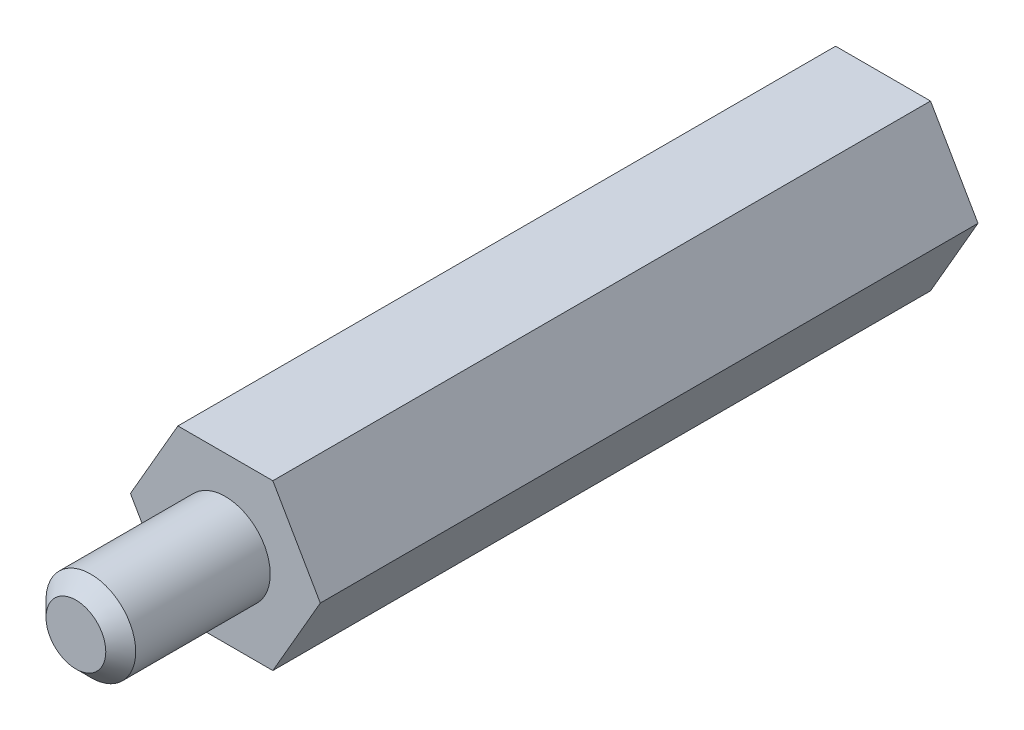
SolidWorks part; units mm, degrees
material "黄铜"
ref_plane "前视基准面" through (0, 0, 0) normal (0, 0, 1) x (1, 0, 0)
ref_plane "上视基准面" through (0, 0, 0) normal (0, 1, 0) x (1, 0, 0)
ref_plane "右视基准面" through (0, 0, 0) normal (1, 0, 0) x (0, 0, -1)
sketch "草图1" plane through (0, 0, 0) normal (0, 0, 1) x (1, 0, 0)
  line L1 (3.1754, 0) -> (1.5877, 2.75)
  line L2 (1.5877, 2.75) -> (-1.5877, 2.75)
  line L3 (-1.5877, 2.75) -> (-3.1754, 0)
  line L4 (-3.1754, 0) -> (-1.5877, -2.75)
  line L5 (-1.5877, -2.75) -> (1.5877, -2.75)
  line L6 (1.5877, -2.75) -> (3.1754, 0)
  circle A0 centre (0, 0) radius 2.75 construction
extrude "凸台-拉伸1" add sketch "草图1" along normal blind 22
sketch "草图2" plane through (0, 0, 22) normal (0, 0, 1) x (1, 0, 0)
  circle A0 centre (0, 0) radius 1.5
extrude "凸台-拉伸2" add sketch "草图2" along normal blind 5
chamfer "倒角1" distance 0.5 angle 45 1 edges at (1.5, 0, 27)
sketch "草图3" plane through (0, 0, 0) normal (0, 0, -1) x (-1, 0, 0)
  circle A0 centre (0, 0) radius 1.5
extrude "切除-拉伸1" cut sketch "草图3" against normal blind 10
